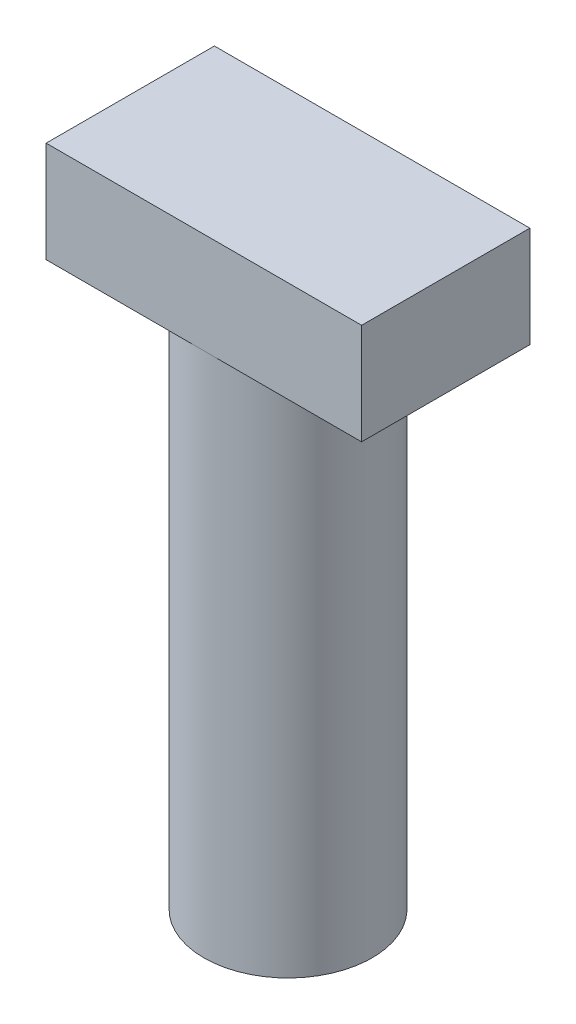
SolidWorks part; units mm, degrees
ref_plane "Alzado" through (0, 0, 0) normal (0, 0, 1) x (1, 0, 0)
ref_plane "Planta" through (0, 0, 0) normal (0, 1, 0) x (1, 0, 0)
ref_plane "Vista lateral" through (0, 0, 0) normal (1, 0, 0) x (0, 0, -1)
sketch "Croquis1" plane through (0, 0, 0) normal (0, 1, 0) x (1, 0, 0)
  circle A0 centre (0, 0) radius 4
  dimension "D1" = 8
extrude "Saliente-Extruir1" add sketch "Croquis1" along normal blind 25
sketch "Croquis2" plane through (0, 25, 0) normal (0, 1, 0) x (1, 0, 0)
  line L1 (-7.5, -4) -> (7.5, -4)
  line L2 (-7.5, -4) -> (-7.5, 4)
  line L3 (-7.5, 4) -> (7.5, 4)
  line L4 (7.5, -4) -> (7.5, 4)
  line L5 (-7.5, -4) -> (7.5, 4) construction
  line L6 (-7.5, 4) -> (7.5, -4) construction
  circle A0 centre (0, 0) radius 4 construction
  point P0 (0, 0)
  dimension "D1" = 15
extrude "Saliente-Extruir2" add sketch "Croquis2" along normal blind 4.8
